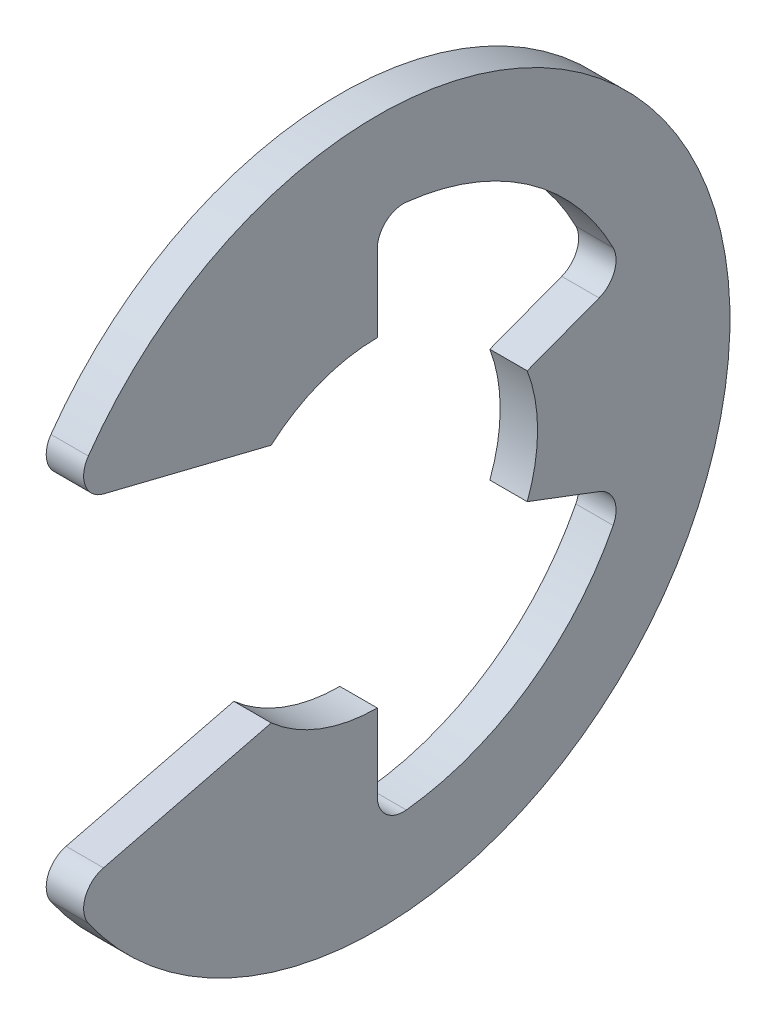
SolidWorks part; units mm, degrees
material "Plain Carbon Steel"
ref_plane "Front" through (0, 0, 0) normal (0, 0, 1) x (1, 0, 0)
ref_plane "Top" through (0, 0, 0) normal (0, 1, 0) x (1, 0, 0)
ref_plane "Right" through (0, 0, 0) normal (1, 0, 0) x (0, 0, -1)
sketch "Sketch1" plane through (0, 0, 0) normal (1, 0, 0) x (0, 0, -1)
  line L0 (-7.3368, -4.0533) -> (-2.5201, -2.8575)
  line L1 (-7.3368, 4.0533) -> (-2.5201, 2.8575)
  line L2 (0, -3.81) -> (0, -6.2926)
  line L3 (0, 3.81) -> (0, 6.2926)
  line L4 (3.5639, -1.347) -> (5.8862, -2.2248)
  line L5 (3.5639, 1.347) -> (5.8862, 2.2248)
  line L6 (0, 0) -> (-8.636, 0) construction
  line L7 (3.5639, 1.347) -> (3.5639, -1.347) construction
  line L8 (0, -3.81) -> (-2.5201, -2.8575) construction
  line L9 (0, 8.382) -> (0, -8.382) construction
  circle A1 centre (0, 0) radius 8.636 construction
  circle A2 centre (0, 0) radius 3.81 construction
  arc A3 (-7.3368, -4.0533) -> (-7.3368, 4.0533) centre (0, 0) ccw
  arc A4 (-2.5201, -2.8575) -> (0, -3.81) centre (0, 0) ccw
  arc A5 (-2.5201, 2.8575) -> (0, 3.81) centre (0, 0) cw
  arc A6 (3.5639, 1.347) -> (3.5639, -1.347) centre (0, 0) cw
  arc A7 (0, -6.2926) -> (5.8862, -2.2248) centre (0, 0) ccw
  arc A8 (5.8862, 2.2248) -> (0, 6.2926) centre (0, 0) ccw
  dimension "D1" = 6.2926
  dimension "OD" = 16.764
  dimension "L" = 17.272
  dimension "D" = 7.62
  dimension "D2" = 4.3322
  dimension "D3" = 5.715
extrude "Extrude1" add sketch "Sketch1" along normal mid plane 0.889
fillet "Fillet1" radius 0.6223 6 edges at (0, -6.2926, 0) (0, 6.2926, 0) (0, -4.0533, 7.3368) (0, 4.0533, 7.3368) (0, -2.2248, -5.8862) (0, 2.2248, -5.8862)
sketch "Sketch3" plane through (0, 0, 0) normal (0, 1, 0) x (1, 0, 0)
  line L0 (0.4953, 4.7625) -> (0.4953, 3.8481)
  line L1 (0.4953, 3.8481) -> (-0.4953, 3.8481)
  line L2 (-0.4953, 3.8481) -> (-0.4953, 4.7625)
  line L3 (-0.4953, 4.7625) -> (-10.6489, 4.7625)
  line L4 (4.21, 0) -> (4.21, 4.3053)
  line L5 (-10.6489, 4.7625) -> (-10.6489, 0)
  line L6 (-10.6489, 0) -> (4.21, 0)
  line L8 (4.21, 0) -> (4.21, 4.7625) construction
  line L9 (4.21, 4.7625) -> (0.4953, 4.7625) construction
  line L10 (4.21, 0) -> (17.2631, 0) construction
  line L11 (4.21, 4.3053) -> (3.7528, 4.7625)
  line L12 (3.7528, 4.7625) -> (0.4953, 4.7625)
  point P2 (0, 3.8481)
  point P5 (0.4953, 4.3053)
  dimension "D1" = 3.7147
  dimension "Ds" = 9.525
  dimension "Dg" = 7.6962
  dimension "W" = 0.9906
  dimension "D2" = 14.859
  dimension "D3" = 45
revolve "Revolve2" [suppressed] add sketch "Sketch3" angle 360 about L10
equation "\"D2@Sketch3\" = \"W@Sketch3\"*15"
equation "\"D1@Sketch3\" = \"D2@Sketch3\"/4"
equation "\"D1@Sketch1\" = (\"OD@Sketch1\"+\"D@Sketch1\")/3.875"
equation "\"D3@Sketch1\" = \"D@Sketch1\"*.75"
equation "\"D1@Fillet1\" = \"D1@Extrude1\"*.7"
